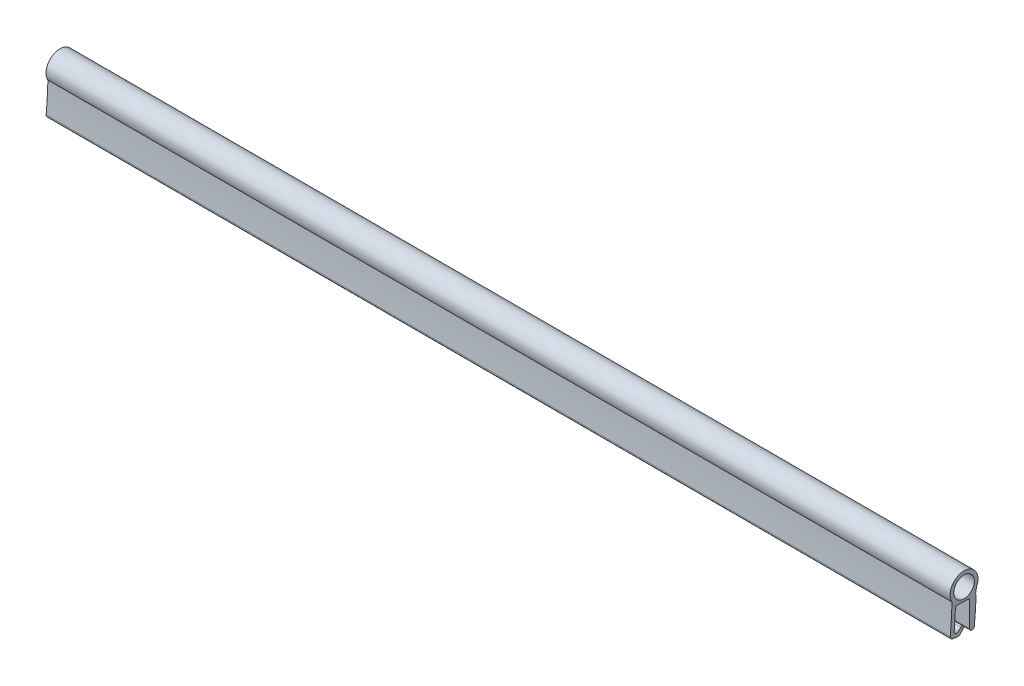
SolidWorks part; units mm, degrees
ref_plane "Plan de face" through (0, 0, 0) normal (0, 0, 1) x (1, 0, 0)
ref_plane "Plan de dessus" through (0, 0, 0) normal (0, 1, 0) x (1, 0, 0)
ref_plane "Plan de droite" through (0, 0, 0) normal (1, 0, 0) x (0, 0, -1)
sketch "Esquisse1" plane through (0, 0, 0) normal (1, 0, 0) x (0, 0, -1)
  line L0 (-0.0365, -2.3383) -> (-0.0166, -1.7529)
  line L1 (21.1727, -7.5) -> (-42.9122, -7.5) construction
  line L2 (21.1727, 7.5) -> (-42.9122, 7.5) construction
  line L3 (0, -20.6998) -> (0, 49.585) construction
  line L4 (-75, -4.7823) -> (-75, 49.585) construction
  line L5 (-75, 0) -> (-0.3759, -7.5) construction
  line L6 (-75, 0) -> (4.0977, 2.6781) construction
  line L8 (-1.0962, 16.7097) -> (-1.0962, -10.2001) construction
  line L17 (-3.1517, -2.6828) -> (-1.3861, -2.7426)
  line L18 (-3.406, -6.5924) -> (-3.1733, -6.6158)
  line L19 (-4.3559, -8.7961) -> (-4.3559, -4.9834) construction
  line L20 (-2.8559, -6.0442) -> (-2.8559, -8.7961) construction
  line L21 (-1.0962, -7.0843) -> (-1.0962, -3.0424)
  line L22 (-3.8601, -7.1498) -> (-2.9974, -7.2365)
  line L27 (-3.5498, 14.9531) -> (-3.5498, -2.6693) construction
  line L35 (-0.2428, -2.5311) -> (-0.05, -2.7375)
  line L36 (-2.0354, -2.2203) -> (-2.0354, 2.2203) construction
  line L38 (-2.8559, -7.2508) -> (-1.6495, -6.0443) construction
  line L39 (-2.1654, -6.5603) -> (-3.1638, -5.5619) construction
  line L40 (-2.4074, -5.9537) -> (-3.3172, -6.8635) construction
  line L41 (-2.5897, -6.136) -> (-3.0119, -6.5583)
  line L42 (-2.0371, -6.0077) -> (-2.6593, -6.6299) construction
  line L43 (-2.1654, -6.5603) -> (-2.7553, -7.1502)
  line L45 (-0.0365, -2.3383) -> (-0.2428, -2.5311)
  arc A0 (-0.3388, -7.1203) -> (-0.05, -2.7375) centre (-75, 0) ccw
  circle A1 centre (-2.0354, -0.6508) radius 1.7
  arc A2 (-4.308, -6.6058) -> (-4.023, -1.8082) centre (-75, 0) ccw
  arc A3 (-0.0166, -1.7529) -> (-4.023, -1.8082) centre (-2.0354, -0.6508) ccw
  arc A4 (-3.4616, -2.9702) -> (-3.1517, -2.6828) centre (-3.1619, -2.9826) cw
  arc A5 (-3.4616, -2.9702) -> (-3.6749, -6.2677) centre (-75, 0) cw
  arc A16 (-1.0962, -7.0843) -> (-0.3388, -7.1203) centre (-0.7166, -7.0843) ccw
  arc A17 (-3.6749, -6.2677) -> (-3.406, -6.5924) centre (-3.376, -6.2939) ccw
  arc A18 (-1.3861, -2.7426) -> (-1.0962, -3.0424) centre (-1.3962, -3.0424) cw
  arc A22 (-4.308, -6.6058) -> (-3.8601, -7.1498) centre (-3.8101, -6.6523) ccw
  arc A27 (-3.1733, -6.6158) -> (-3.0119, -6.5583) centre (-3.1533, -6.4168) ccw
  arc A28 (-2.7553, -7.1502) -> (-2.9974, -7.2365) centre (-2.9674, -6.938) cw
  circle A29 centre (-75, 0) radius 74.8 construction
  arc A33 (-2.1654, -6.5603) -> (-2.5897, -6.136) centre (-2.3775, -6.3481) ccw
  point P85 (-1.0962, -2.7524)
  point P102 (-4.3559, -7.1)
  point P117 (-3.079, -6.6253)
  dimension "D12" = 0.3
  dimension "D20" = 0.6
  dimension "D21" = 0.3
  dimension "D22" = 0.9
  dimension "D23" = 0.3
  dimension "D15" = 0.5
  dimension "D17" = 0.2
  dimension "D1" = 15
  dimension "D18" = 45
  dimension "D19" = 1.5
extrude "Boss.-Extru.3" add sketch "Esquisse1" along normal blind 149
